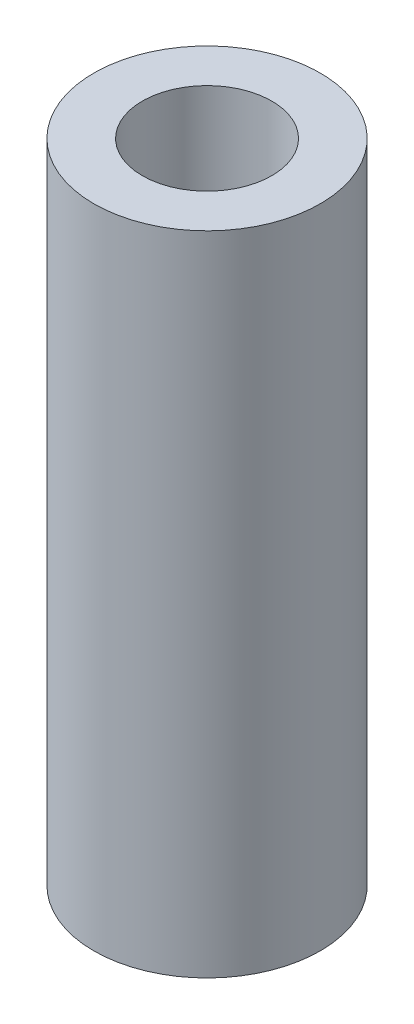
SolidWorks part; units mm, degrees
material "AISI 316 Annealed Stainless Steel Bar (SS)"
ref_plane "Front Plane" through (0, 0, 0) normal (0, 0, 1) x (1, 0, 0)
ref_plane "Top Plane" through (0, 0, 0) normal (0, 1, 0) x (1, 0, 0)
ref_plane "Right Plane" through (0, 0, 0) normal (1, 0, 0) x (0, 0, -1)
sketch "Sketch1" plane through (0, 0, 0) normal (0, 1, 0) x (1, 0, 0)
  circle A0 centre (0, 0) radius 40
  circle A1 centre (0, 0) radius 70
  dimension "D1" = 140
  dimension "D2" = 80
extrude "Boss-Extrude1" add sketch "Sketch1" along normal blind 400
